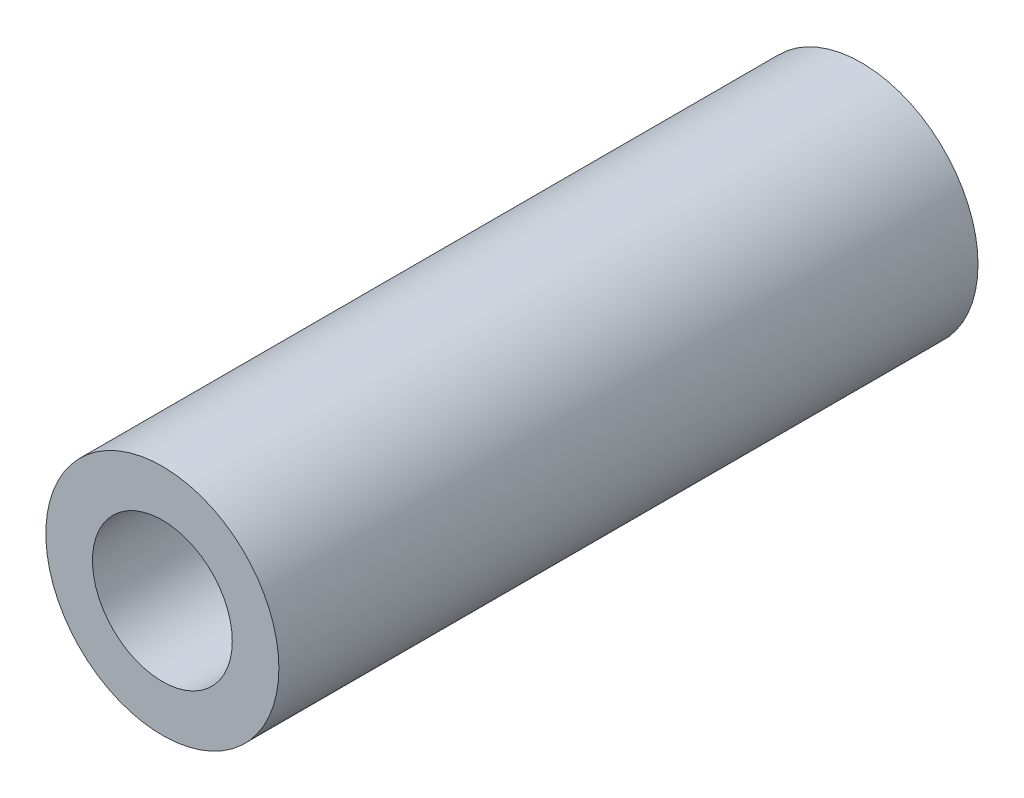
SolidWorks part; units mm, degrees
material "1.7223 (41CrMo4)"
ref_plane "Alzado" through (0, 0, 0) normal (0, 0, 1) x (1, 0, 0)
ref_plane "Planta" through (0, 0, 0) normal (0, 1, 0) x (1, 0, 0)
ref_plane "Vista lateral" through (0, 0, 0) normal (1, 0, 0) x (0, 0, -1)
sketch "Croquis2" plane through (0, 0, 0) normal (0, 1, 0) x (1, 0, 0)
  line L0 (0, 0) -> (0, 25) construction
  line L1 (-1.5, 10) -> (-2.5, 10)
  line L2 (-2.5, 10) -> (-2.5, 25)
  line L3 (-2.5, 25) -> (-1, 25)
  line L4 (-1.5, 10) -> (-1.5, 12.3)
  line L6 (-2, 12.8) -> (-2, 24.5)
  line L7 (-2, 24.5) -> (-1, 24.5)
  line L9 (-1.25, 25.5) -> (1.25, 25.5) construction
  line L10 (-2, 12.8) -> (-1, 12.8)
  line L12 (-1.5, 12.3) -> (-1, 12.3)
  line L13 (-1, 12.8) -> (-1, 12.3)
  line L17 (-1, 25) -> (-1, 24.5)
  line L18 (13, 10.8) -> (-13, 10.8) construction
  line L19 (-2.5, 10) -> (2.5, 10) construction
  point P14 (-2.5, 1.8569)
  dimension "D1" = 3
  dimension "D2" = 0.5
  dimension "D3" = 5
  dimension "D4" = 1.5
  dimension "D5" = 4
  dimension "D6" = 0.5
  dimension "D7" = 0.5
revolve "Revolución1" add sketch "Croquis2" angle 360 about L0
